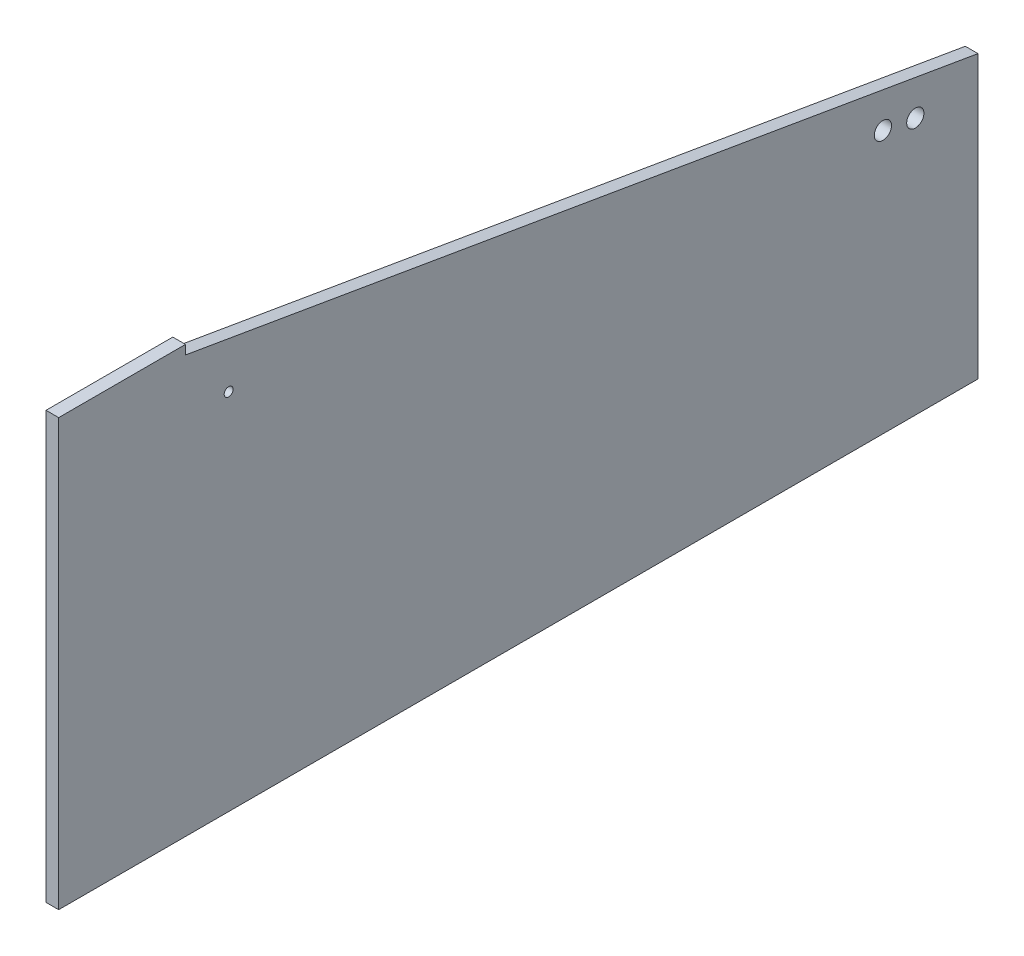
SolidWorks part; units mm, degrees
ref_plane "Front Plane" through (0, 0, 0) normal (0, 0, 1) x (1, 0, 0)
ref_plane "Top Plane" through (0, 0, 0) normal (0, 1, 0) x (1, 0, 0)
ref_plane "Right Plane" through (0, 0, 0) normal (1, 0, 0) x (0, 0, -1)
sketch "Sketch1" plane through (0, 0, 0) normal (1, 0, 0) x (0, 0, -1)
  line L0 (0, 0) -> (0, 605)
  line L1 (0, 605) -> (180, 605)
  line L2 (180, 605) -> (180, 592)
  line L3 (180, 592) -> (1305, 400)
  line L4 (1305, 400) -> (1305, 0)
  line L5 (1305, 0) -> (0, 0)
  line L6 (1170, 373.04) -> (1170, 582.9795) construction
  line L7 (1216, 365.1893) -> (1216, 573.7056) construction
  circle A0 centre (1216, 365.1893) radius 12.25
  circle A1 centre (1170, 373.04) radius 12.25
  point P13 (1170, 423.04)
  point P14 (1216, 415.1893)
  dimension "D6" = 89
  dimension "D7" = 50
  dimension "D8" = 24.5
  dimension "D9" = 135
  dimension "D10" = 24.5
  dimension "D1" = 605
  dimension "D2" = 180
  dimension "D3" = 13
  dimension "D4" = 1305
  dimension "D5" = 400
  dimension "D11" = 50
extrude "Boss-Extrude1" add sketch "Sketch1" along normal blind 18
sketch "Sketch2" plane through (18, 0, 0) normal (1, 0, 0) x (0, 0, -1)
  line L0 (0, 605) -> (0, 0) construction
  line L1 (180, 605) -> (0, 605) construction
  circle A0 centre (241.3, 516.1) radius 6.35
  dimension "D1" = 241.3
  dimension "D2" = 88.9
  dimension "D3" = 12.7
extrude "Cut-Extrude1" cut sketch "Sketch2" against normal blind 40
